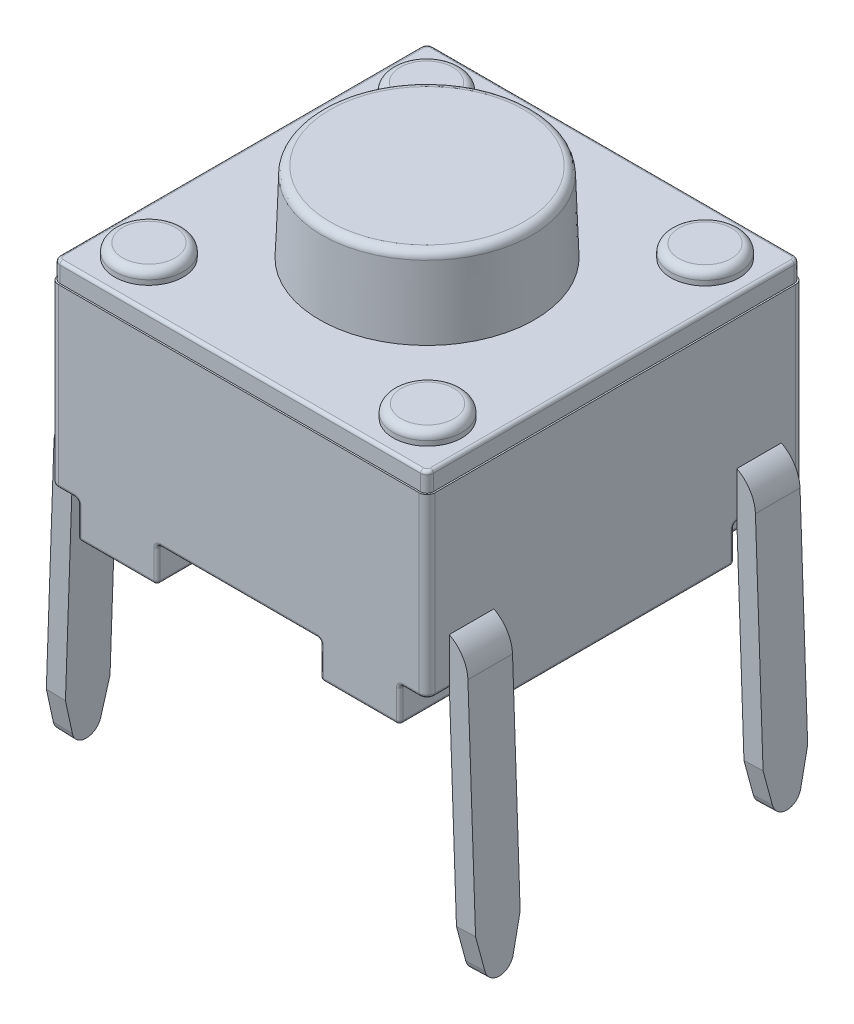
SolidWorks part; units mm, degrees
ref_plane "Front Plane" through (0, 0, 0) normal (0, 0, 1) x (1, 0, 0)
ref_plane "Top Plane" through (0, 0, 0) normal (0, 1, 0) x (1, 0, 0)
ref_plane "Right Plane" through (0, 0, 0) normal (1, 0, 0) x (0, 0, -1)
sketch "Sketch1" plane through (0, 0, 0) normal (0, 1, 0) x (1, 0, 0)
  line L1 (-3.0035, -3.0035) -> (3.0035, -3.0035)
  line L2 (-3.0035, -3.0035) -> (-3.0035, 3.0036)
  line L3 (-3.0035, 3.0036) -> (3.0035, 3.0036)
  line L4 (3.0035, -3.0035) -> (3.0035, 3.0036)
  line L5 (-3.0035, -3.0035) -> (3.0035, 3.0036) construction
  line L6 (-3.0035, 3.0036) -> (3.0035, -3.0035) construction
  point P0 (0, 0)
  dimension "D1" = 6.0071
  dimension "D2" = 6.0071
extrude "Boss-Extrude1" add sketch "Sketch1" along normal blind 2.8194 from offset 0.5588
fillet "Fillet1" radius 0.127 4 edges at (-3.0035, 1.9685, 3.0035) (-3.0035, 1.9685, -3.0036) (3.0035, 1.9685, -3.0036) (3.0035, 1.9685, 3.0035)
sketch "Sketch2" plane through (0, 3.3782, 0) normal (0, -1, 0) x (-1, 0, 0)
  line L8 (2.9781, -2.8765) -> (2.9781, 2.8765)
  line L9 (-2.8765, -2.9781) -> (2.8765, -2.9781)
  line L10 (-2.9781, 2.8765) -> (-2.9781, -2.8765)
  line L11 (2.8765, 2.9782) -> (-2.8765, 2.9782)
  line L12 (2.9781, -2.8765) -> (2.9781, 2.8765)
  line L13 (-2.8765, -2.9781) -> (2.8765, -2.9781)
  line L14 (-2.9781, 2.8765) -> (-2.9781, -2.8765)
  line L15 (2.8765, 2.9782) -> (-2.8765, 2.9782)
  arc A8 (2.8765, -2.9781) -> (2.9781, -2.8765) centre (2.8765, -2.8765) ccw
  arc A9 (-2.9781, -2.8765) -> (-2.8765, -2.9781) centre (-2.8765, -2.8765) ccw
  arc A10 (-2.8765, 2.9782) -> (-2.9781, 2.8765) centre (-2.8765, 2.8766) ccw
  arc A11 (2.9781, 2.8765) -> (2.8765, 2.9782) centre (2.8765, 2.8765) ccw
  arc A12 (2.8765, -2.9781) -> (2.9781, -2.8765) centre (2.8765, -2.8765) ccw
  arc A13 (-2.9781, -2.8765) -> (-2.8765, -2.9781) centre (-2.8765, -2.8765) ccw
  arc A14 (-2.8765, 2.9782) -> (-2.9781, 2.8765) centre (-2.8765, 2.8766) ccw
  arc A15 (2.9781, 2.8765) -> (2.8765, 2.9782) centre (2.8765, 2.8765) ccw
  dimension "D1" = 0.0254
extrude "Boss-Extrude2" add sketch "Sketch2" against normal blind 0.3048
sketch "Sketch3" plane through (0, 0, 0) normal (0, 1, 0) x (1, 0, 0)
  line L0 (-2.5662, -3.0035) -> (-2.5662, -1.8948)
  line L1 (-2.8765, -3.0035) -> (2.8765, -3.0035) construction
  line L2 (-2.5662, -1.8948) -> (-3.0035, -1.8948)
  line L3 (-3.0035, 2.8765) -> (-3.0035, -2.8765) construction
  line L4 (-2.4413, -0.5609) -> (-1.3018, -0.5609)
  line L5 (-1.3018, -0.5609) -> (-1.3017, -3.0035)
  line L6 (-2.4413, -0.5609) -> (-2.4413, 0.5609)
  line L7 (-2.5662, -3.0035) -> (-1.3017, -3.0035)
  line L8 (-3.0035, -1.8948) -> (-3.0035, 1.8948)
  line L9 (-2.4413, 0) -> (-3.0035, 0) construction
  line L10 (-2.5662, 3.0036) -> (-1.3017, 3.0035)
  line L11 (-1.3017, 0.5609) -> (-1.3017, 3.0035)
  line L12 (-2.4413, 0.5609) -> (-1.3017, 0.5609)
  line L13 (-2.5662, 1.8948) -> (-3.0035, 1.8948)
  line L14 (-2.5662, 3.0036) -> (-2.5662, 1.8948)
  line L15 (0, -3.0035) -> (0, 3.0036) construction
  line L16 (2.8765, 3.0036) -> (-2.8765, 3.0036) construction
  line L17 (2.4413, 0) -> (3.0035, 0) construction
  line L18 (2.5662, 3.0035) -> (2.5662, 1.8948)
  line L19 (2.5662, 1.8948) -> (3.0035, 1.8948)
  line L20 (2.4413, 0.5609) -> (1.3017, 0.5609)
  line L21 (1.3017, 0.5609) -> (1.3017, 3.0035)
  line L22 (2.5662, 3.0035) -> (1.3017, 3.0035)
  line L23 (3.0035, -1.8948) -> (3.0035, 1.8948)
  line L24 (2.5662, -3.0036) -> (1.3017, -3.0036)
  line L25 (2.4413, -0.5609) -> (2.4413, 0.5609)
  line L26 (1.3017, -0.5609) -> (1.3017, -3.0036)
  line L27 (2.4413, -0.5609) -> (1.3017, -0.5609)
  line L28 (2.5662, -1.8948) -> (3.0035, -1.8948)
  line L29 (2.5662, -3.0036) -> (2.5662, -1.8948)
  dimension "D1" = 1.7018
extrude "Boss-Extrude3" add sketch "Sketch3" along normal up to next
sketch "Sketch4" plane through (0, 3.683, 0) normal (0, 1, 0) x (1, 0, 0)
  line L1 (-2.2217, -2.2129) -> (2.2217, -2.2129) construction
  line L2 (-2.2217, -2.2129) -> (-2.2217, 2.2129) construction
  line L3 (-2.2217, 2.2129) -> (2.2217, 2.2129) construction
  line L4 (2.2217, -2.2129) -> (2.2217, 2.2129) construction
  line L5 (-2.2217, -2.2129) -> (2.2217, 2.2129) construction
  line L6 (-2.2217, 2.2129) -> (2.2217, -2.2129) construction
  circle A0 centre (2.2217, 2.2129) radius 0.5461
  circle A1 centre (-2.2217, 2.2129) radius 0.5461
  circle A2 centre (-2.2217, -2.2129) radius 0.5461
  circle A3 centre (2.2217, -2.2129) radius 0.5461
  point P0 (0, 0)
  dimension "D1" = 1.0922
extrude "Boss-Extrude4" add sketch "Sketch4" along normal blind 0.2032
sketch "Sketch5" plane through (0, 3.683, 0) normal (0, 1, 0) x (1, 0, 0)
  circle A0 centre (0, 0) radius 1.7145
  dimension "D1" = 3.429
extrude "Boss-Extrude5" add sketch "Sketch5" along normal blind 1.27 draft 2
fillet "Fillet2" radius 0.127 5 edges at (-2.2217, 3.8862, -1.6668) (-2.2217, 3.8862, 2.759) (2.2217, 3.8862, -1.6668) (2.2217, 3.8862, 2.759) (0, 4.953, 1.6702)
fillet "Fillet3" radius 0.0508 88 edges at (2.9664, 0.5588, 2.9664) (2.9664, 0.5588, -2.9664) (-2.9664, 0.5588, -2.9664) (-2.9664, 0.5588, 2.9664) (3.0035, 0.5588, 2.3857) (3.0035, 0.5588, -2.3857) (1.3017, 0.2794, 3.0036) (1.3017, 0.2794, -3.0035) (2.9484, 3.683, -2.9484) (0, 3.683, -2.9782) (-2.9484, 3.683, -2.9484) (-2.9781, 3.683, 0) (-2.9484, 3.683, 2.9484) (0, 3.683, 2.9781) (2.9484, 3.683, 2.9484) (2.4413, 0.2794, 0.5609) (1.3017, 0.2794, 0.5609) (1.3017, 0.2794, -0.5609) (2.4413, 0.2794, -0.5609) (-1.3018, 0.2794, 0.5609) (-2.4413, 0.2794, 0.5609) (-2.4413, 0.2794, -0.5609) (-1.3017, 0.2794, -0.5609) (2.7849, 0.5588, 1.8948) (3.0035, 0.2794, 1.8948) (2.5662, 0.2794, 3.0036) (2.5662, 0.5588, 2.4492) (2.5662, 0.2794, 1.8948) (3.0035, 0.2794, -1.8948) (2.7849, 0.5588, -1.8948) (2.5662, 0.2794, -1.8948) (2.5662, 0.5588, -2.4492) (2.5662, 0.2794, -3.0035) (-2.5662, 0.2794, -1.8948) (-2.5662, 0.2794, 1.8948) (-1.8715, 0.5588, -0.5609) (-2.4413, 0.5588, 0) (-1.8715, 0.5588, 0.5609) (1.3017, 0.5588, 1.7822) (1.8715, 0.5588, 0.5609) (2.4413, 0.5588, 0) (1.8715, 0.5588, -0.5609) (1.3017, 0.5588, -1.7822) (-1.3017, 0, 1.7822) (-1.8715, 0, 0.5609) (-2.4413, 0, 0) (-1.8715, 0, -0.5609) (-1.3017, 0, -1.7822) (-1.934, 0, -3.0035) (-2.5662, 0, -2.4492) (-2.7849, 0, -1.8948) (-3.0035, 0, 0) (-2.7849, 0, 1.8948) (-2.5662, 0, 2.4492) (-1.934, 0, 3.0035) (1.3017, 0, -1.7822) (1.8715, 0, -0.5609) (2.4413, 0, 0) (1.8715, 0, 0.5609) (1.3017, 0, 1.7822) (1.934, 0, 3.0036) (2.5662, 0, 2.4492) (2.7849, 0, 1.8948) (3.0035, 0, 0) (2.7849, 0, -1.8948) (2.5662, 0, -2.4492) (1.934, 0, -3.0035) (2.9781, 3.683, 0)
sketch "Sketch6" plane through (0, 0, 3.0035) normal (0, 0, 1) x (1, 0, 0)
  line L0 (-2.9873, 1.0641) -> (-3.0423, -0.5107)
  line L3 (-3.1132, -2.5415) -> (-3.1424, -3.3782)
  line L4 (-2.9873, 1.0641) -> (-2.5265, 1.0641)
  line L5 (-1.3525, 0) -> (-2.5154, 0) construction
  line L6 (-3.0423, -0.5107) -> (-3.1132, -2.5415)
  dimension "D1" = 4.445
  dimension "D2" = 3.3782
  dimension "D3" = 3.0226
  dimension "D5" = 2.032
  dimension "D6" = 1.5748
  dimension "D7" = 92
extrude "Extrude-Thin1" add sketch "Sketch6" against normal blind 0.7112 from offset 0.3556 thin offset against normal yes
sketch "Sketch9" plane through (-3.3254, 0.1161, 0) normal (-0.9994, 0.0349, 0) x (0, 0, 1)
  line L0 (2.6479, -2.7766) -> (2.5175, -3.3091)
  line L1 (2.0672, -3.3091) -> (1.9367, -2.7766)
  line L2 (1.9367, -3.4858) -> (2.6479, -3.4858) construction
  line L3 (2.6479, -2.7766) -> (2.6479, -3.4858)
  line L4 (2.6479, -3.4858) -> (1.9367, -3.4858)
  line L5 (1.9367, -3.4858) -> (1.9367, -2.7766)
  line L6 (1.9367, -3.4858) -> (1.9367, 0.7139) construction
  line L7 (2.6479, -3.4858) -> (2.6479, 0.7139) construction
  arc A0 (2.5175, -3.3091) -> (2.0672, -3.3091) centre (2.2923, -3.254) cw
  line M1 (2.6479, -3.4858) -> (2.6479, 0.7139)
  line M3 (1.9367, 0.7139) -> (1.9367, -3.4858)
  line M4 (1.9367, -3.4858) -> (2.6479, -3.4858)
extrude "Cut-Extrude1" cut sketch "Sketch9" against normal blind 0.7112 contours L0 A0 L4 M1 | A0 L1 M4 M3
mirror "Mirror1" about plane through (0, 0, 0) normal (0, 0, 1) of "Cut-Extrude1", "Extrude-Thin1"
mirror "Mirror3" about plane through (0, 0, 0) normal (1, 0, 0) of "Mirror1", "Cut-Extrude1", "Extrude-Thin1"
